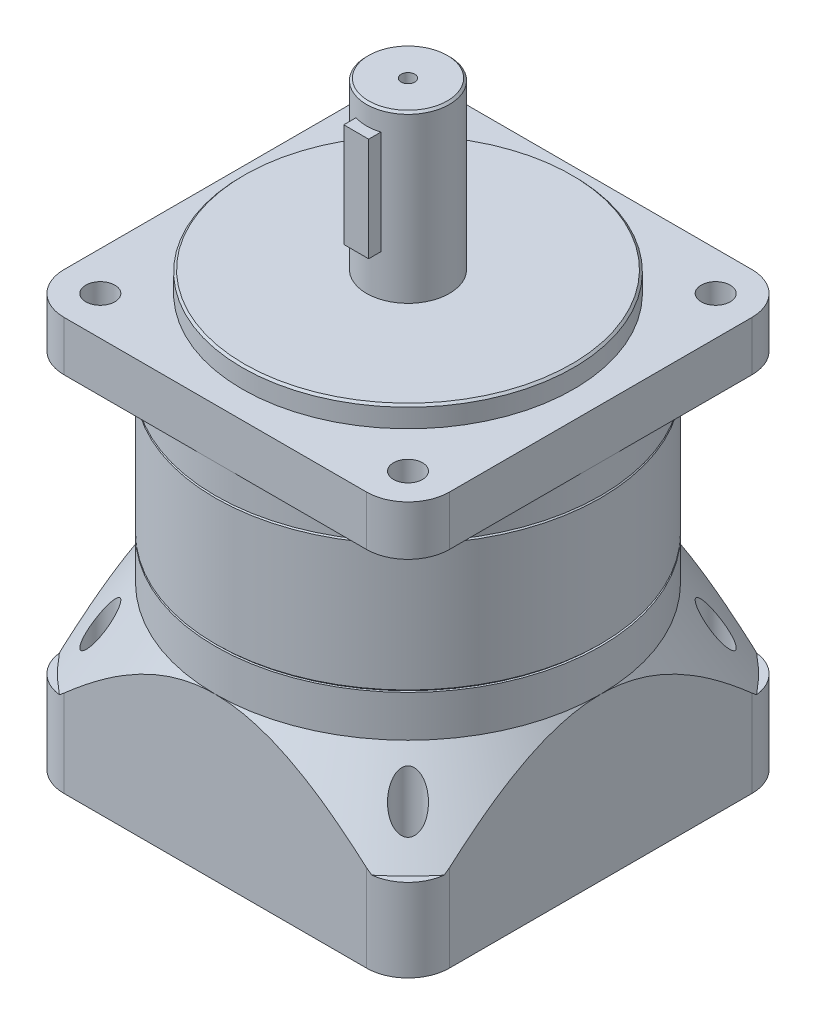
SolidWorks part; units mm, degrees
ref_plane "前基準面" through (0, 0, 0) normal (0, 0, 1) x (1, 0, 0)
ref_plane "上基準面" through (0, 0, 0) normal (0, 1, 0) x (1, 0, 0)
ref_plane "右基準面" through (0, 0, 0) normal (1, 0, 0) x (0, 0, -1)
sketch "草圖1" plane through (0, 0, 0) normal (0, 1, 0) x (1, 0, 0)
  line L1 (-36.5, -46.5) -> (36.5, -46.5)
  line L2 (-46.5, -36.5) -> (-46.5, 36.5)
  line L3 (-36.5, 46.5) -> (36.5, 46.5)
  line L4 (46.5, -36.5) -> (46.5, 36.5)
  line L5 (-46.5, -46.5) -> (46.5, 46.5) construction
  line L6 (-46.5, 46.5) -> (46.5, -46.5) construction
  arc A0 (36.5, -46.5) -> (46.5, -36.5) centre (36.5, -36.5) ccw
  arc A1 (-36.5, -46.5) -> (-46.5, -36.5) centre (-36.5, -36.5) cw
  arc A2 (36.5, 46.5) -> (46.5, 36.5) centre (36.5, 36.5) cw
  arc A3 (-46.5, 36.5) -> (-36.5, 46.5) centre (-36.5, 36.5) cw
  point P0 (0, 0)
  dimension "D3" = 10
  dimension "D1" = 93
  dimension "D2" = 93
extrude "填料-伸長1" add sketch "草圖1" along normal blind 49
sketch "草圖2" plane through (0, 49, 0) normal (0, 1, 0) x (1, 0, 0)
  circle A0 centre (0, 0) radius 46.5
extrude "除料-伸長3" cut sketch "草圖2" along normal blind 10 and the other way blind 19 draft 35 from offset 10 flip side to cut offset against normal yes
sketch "草圖3" plane through (0, 49, 0) normal (0, 1, 0) x (1, 0, 0)
  circle A0 centre (0, 0) radius 46.5
extrude "填料-伸長2" add sketch "草圖3" along normal blind 31.5 separate body
sketch "草圖4" plane through (0, 80.5, 0) normal (0, 1, 0) x (1, 0, 0)
  circle A0 centre (0, 0) radius 46.5
extrude "填料-伸長3" add sketch "草圖4" along normal blind 19 separate body
chamfer "導角1" distance 0.5 angle 45 2 edges at (0, 80.5, 46.5) (0, 49, 46.5)
sketch "草圖6" plane through (0, 99.5, 0) normal (0, 1, 0) x (1, 0, 0)
  circle A0 centre (0, 0) radius 40
  dimension "D1" = 80
extrude "填料-伸長5" add sketch "草圖6" along normal blind 5
sketch "草圖7" plane through (0, 104.5, 0) normal (0, 1, 0) x (1, 0, 0)
  circle A0 centre (0, 0) radius 10
  dimension "D1" = 20
extrude "填料-伸長6" add sketch "草圖7" along normal blind 40
chamfer "導角2" distance 0.5 angle 45 3 edges at (0, 144.5, 10) (0, 99.5, 46.5) (0, 104.5, 40)
sketch "草圖10" plane through (0, 0, 0) normal (0, 0, 1) x (1, 0, 0)
  line L0 (9.5, 144.5) -> (-9.5, 144.5) construction
  line L1 (-3, 139.5) -> (3, 139.5)
  line L2 (-3, 139.5) -> (-3, 114.5)
  line L3 (-3, 114.5) -> (3, 114.5)
  line L4 (3, 139.5) -> (3, 114.5)
  line L5 (0, -51.15) -> (0, 51.15) construction
  dimension "D1" = 5
  dimension "D2" = 6
  dimension "D3" = 3
  dimension "D4" = 25
extrude "填料-伸長7" add sketch "草圖10" along normal blind 12.5
sketch "草圖11" plane through (0, 0, 0) normal (0, -1, 0) x (1, 0, 0)
  circle A0 centre (0, 0) radius 35
  dimension "D1" = 70
extrude "除料-伸長4" cut sketch "草圖11" against normal blind 6
sketch "草圖12" plane through (0, 6, 0) normal (0, -1, 0) x (1, 0, 0)
  circle A0 centre (0, 0) radius 10
  dimension "D1" = 20
extrude "除料-伸長5" cut sketch "草圖12" against normal blind 40
hole_wizard "M4x0.7 螺紋孔1" positions "草圖14" profile "草圖13" tap size "M4x0.7" standard "JIS"
sketch "草圖14" plane through (0, 144.5, 0) normal (0, 1, 0) x (1, 0, 0)
  point P0 (0, 0)
sketch "草圖13" plane through (0, 144.5, 0) normal (1, 0, 0) x (0, 0, 1)
  line L0 (0, 0) -> (0, 11.0914)
  line L1 (0, 11.0914) -> (1.65, 10.1)
  line L2 (1.65, 10.1) -> (1.65, 0)
  line L5 (1.65, 0) -> (0, 0)
  line L10 (0, 11.0914) -> (-1.65, 10.1) construction
  line L11 (0, -6.35) -> (0, 107.95) construction
  dimension "螺孔鑽直徑" = 3.3
  dimension "螺孔鑽深度" = 10.1
  dimension "導頭角度" = 118
cosmetic thread "鑽孔螺紋2" parameters "D1"=8, "D2"=4
sketch "草圖15" plane through (0, 99.5, 0) normal (0, 1, 0) x (1, 0, 0)
  line L1 (-36.5, -46.5) -> (36.5, -46.5)
  line L2 (-46.5, -36.5) -> (-46.5, 36.5)
  line L3 (-36.5, 46.5) -> (36.5, 46.5)
  line L4 (46.5, -36.5) -> (46.5, 36.5)
  line L5 (-46.5, -46.5) -> (46.5, 46.5) construction
  line L6 (-46.5, 46.5) -> (46.5, -46.5) construction
  arc A0 (-36.5, -46.5) -> (-46.5, -36.5) centre (-36.5, -36.5) cw
  arc A1 (36.5, -46.5) -> (46.5, -36.5) centre (36.5, -36.5) ccw
  arc A2 (36.5, 46.5) -> (46.5, 36.5) centre (36.5, 36.5) cw
  arc A3 (-46.5, 36.5) -> (-36.5, 46.5) centre (-36.5, 36.5) cw
  circle A4 centre (0, 0) radius 44.7565
  point P0 (0, 0)
  dimension "D3" = 10
  dimension "D1" = 93
  dimension "D2" = 93
extrude "填料-伸長8" add sketch "草圖15" against normal blind 12
hole_wizard "Ø7.0 (7) 直徑孔3" positions "草圖17" profile "草圖16" hole size "Ø7.0" standard "JIS" end condition through all
sketch "草圖17" plane through (0, 99.5, 0) normal (0, 1, 0) x (1, 0, 0)
  line L0 (0, 0) -> (37.5471, 37.5471) construction
  line L3 (0, 0) -> (58.2659, 0) construction
  circle A0 centre (0, 0) radius 1.65 construction
  point P0 (37.1231, 37.1231)
  dimension "D1" = 52.5
  dimension "D2" = 45
sketch "草圖16" plane through (37.1231, 99.5, -37.1231) normal (1, 0, 0) x (0, 0, 1)
  line L0 (0, 0) -> (0, 99.5)
  line L1 (0, 99.5) -> (3.5, 99.5)
  line L2 (3.5, 99.5) -> (3.5, 0)
  line L5 (3.5, 0) -> (0, 0)
  line L11 (0, -6.35) -> (0, 107.95) construction
  dimension "貫穿孔直徑" = 7
  dimension "貫穿孔深度" = 99.5
pattern_circular "環狀複製排列1" count 4 over 360 about axis through (0, 0, 0) along (0, 1, 0) of "Ø7.0 (7) 直徑孔3"
